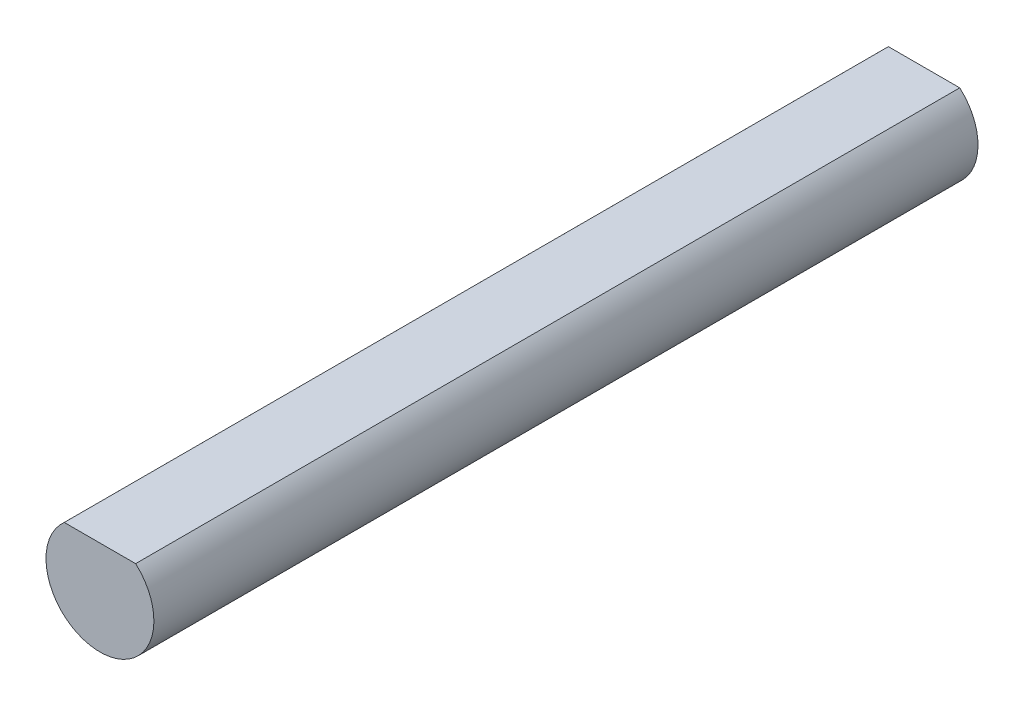
SolidWorks part; units mm, degrees
ref_plane "Front Plane" through (0, 0, 0) normal (0, 0, 1) x (1, 0, 0)
ref_plane "Top Plane" through (0, 0, 0) normal (0, 1, 0) x (1, 0, 0)
ref_plane "Right Plane" through (0, 0, 0) normal (1, 0, 0) x (0, 0, -1)
sketch "Sketch1" plane through (0, 0, 0) normal (0, 0, 1) x (1, 0, 0)
  line L0 (-1.3229, 1.5) -> (1.3229, 1.5)
  arc A0 (-1.3229, 1.5) -> (1.3229, 1.5) centre (0, 0) ccw
  dimension "D1" = 4
  dimension "D2" = 1.5
extrude "Extrude1" add sketch "Sketch1" against normal blind 30.55
